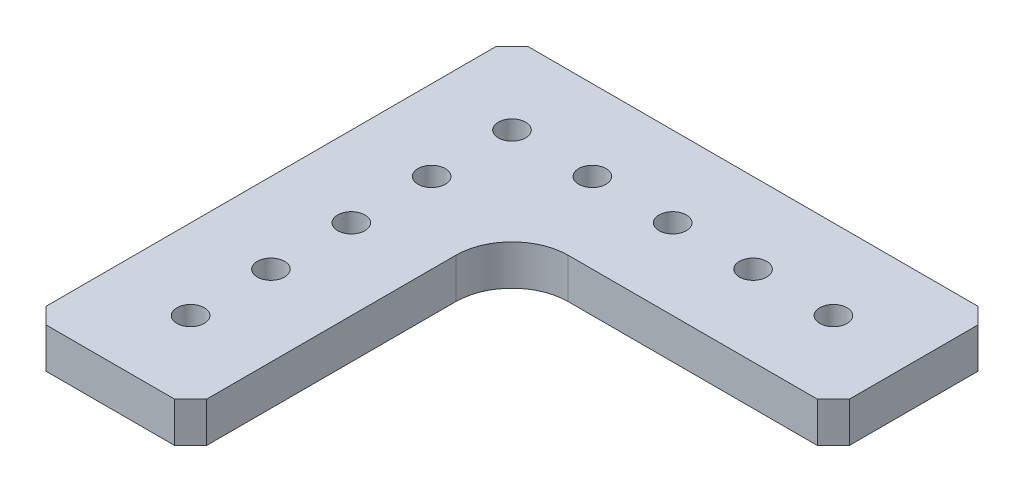
SolidWorks part; units mm, degrees
ref_plane "Front Plane" through (0, 0, 0) normal (0, 0, 1) x (1, 0, 0)
ref_plane "Top Plane" through (0, 0, 0) normal (0, 1, 0) x (1, 0, 0)
ref_plane "Right Plane" through (0, 0, 0) normal (1, 0, 0) x (0, 0, -1)
sketch "Sketch1" plane through (0, 0, 0) normal (0, 1, 0) x (1, 0, 0)
  line L0 (-20.5081, -30.433) -> (-20.5081, 20.367)
  line L1 (-45.9081, 45.767) -> (30.2919, 45.767)
  line L2 (-45.9081, 45.767) -> (-45.9081, 20.367)
  line L4 (30.2919, 45.767) -> (30.2919, 20.367)
  line L5 (-45.9081, 45.767) -> (-20.5081, 45.767)
  line L6 (-45.9081, 45.767) -> (-45.9081, -30.433)
  line L7 (-45.9081, -30.433) -> (-20.5081, -30.433)
  line L9 (-20.5081, 20.367) -> (30.2919, 20.367)
  dimension "D1" = 76.2
  dimension "D2" = 76.2
  dimension "D3" = 50.8
  dimension "D4" = 25.4
extrude "Boss-Extrude1" add sketch "Sketch1" along normal blind 6.35 contours L0 L9 L4 L1 L2 L6 L7
chamfer "Chamfer9" distance 2.54 angle 45 1 edges at (-20.5081, 3.175, 30.433)
chamfer "Chamfer10" distance 2.54 angle 45 1 edges at (30.2919, 3.175, -20.367)
chamfer "Chamfer11" distance 2.54 angle 45 1 edges at (30.2919, 3.175, -45.767)
chamfer "Chamfer12" distance 2.54 angle 45 1 edges at (-45.9081, 3.175, 30.433)
chamfer "Chamfer13" distance 2.54 angle 45 1 edges at (-45.9081, 3.175, -45.767)
fillet "Fillet1" radius 8.89 1 edges at (-20.5081, 3.175, -20.367)
sketch "Sketch2" plane through (0, 6.35, 0) normal (0, 1, 0) x (1, 0, 0)
  line L0 (-43.3681, 45.767) -> (27.7519, 45.767) construction
  line L1 (-45.9081, 43.227) -> (-45.9081, -27.893) construction
  circle A1 centre (-33.2081, 33.067) radius 2.159
  circle A2 centre (-20.5081, 33.067) radius 2.159
  circle A3 centre (-7.8081, 33.067) radius 2.159
  circle A4 centre (4.8919, 33.067) radius 2.159
  circle A5 centre (17.5919, 33.067) radius 2.159
  circle A6 centre (-33.2081, 20.367) radius 2.159
  circle A7 centre (-33.2081, 7.667) radius 2.159
  circle A8 centre (-33.2081, -5.033) radius 2.159
  circle A9 centre (-33.2081, -17.733) radius 2.159
  dimension "D1" = 4.318
  dimension "D2" = 12.7
  dimension "D5" = 4.318
  dimension "D3" = 12.7
  dimension "D6" = 12.7
  dimension "D4" = 5
  dimension "D7" = 4
extrude "Cut-Extrude1" cut sketch "Sketch2" against normal through all contours A1 | A2 | A3 | A4 | A5 | A6 | A7 | A8 | A9
